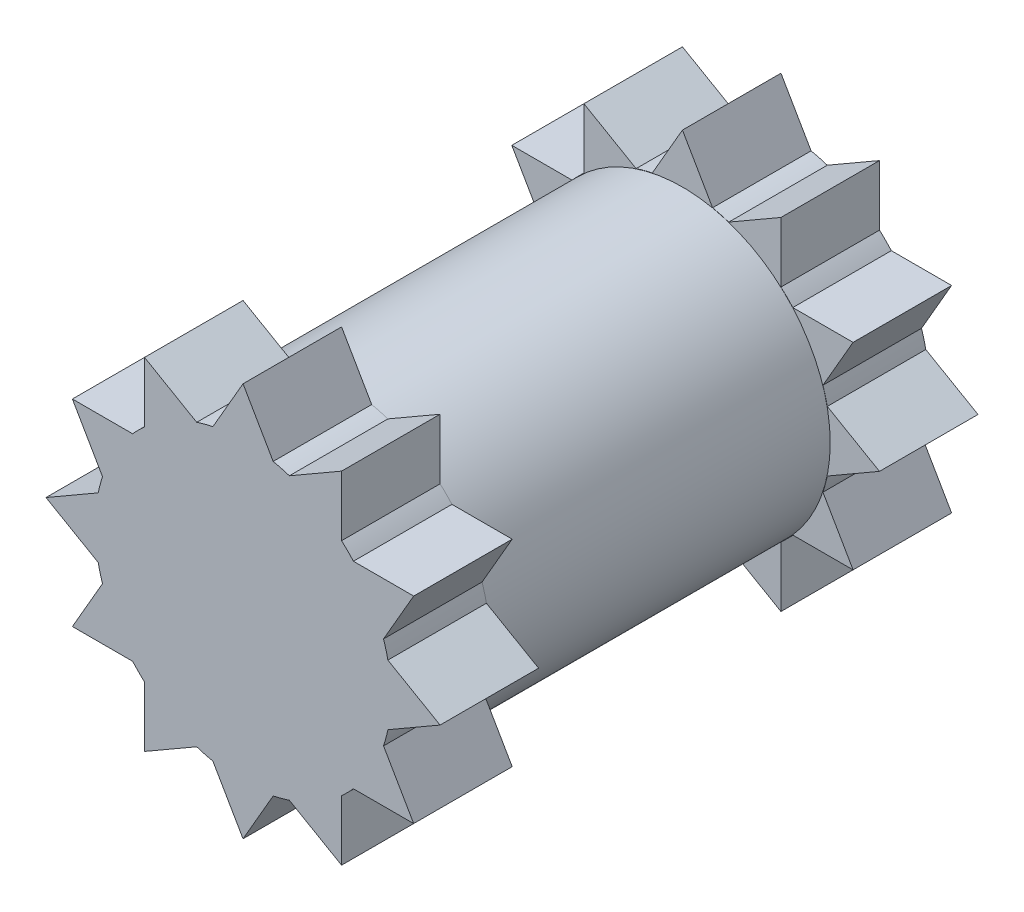
SolidWorks part; units mm, degrees
ref_plane "Ön Düzlem" through (0, 0, 0) normal (0, 0, 1) x (1, 0, 0)
ref_plane "Üst Düzlem" through (0, 0, 0) normal (0, 1, 0) x (1, 0, 0)
ref_plane "Sağ Düzlem" through (0, 0, 0) normal (1, 0, 0) x (0, 0, -1)
sketch "Çizim1" plane through (0, 0, 0) normal (0, 0, 1) x (1, 0, 0)
  circle A0 centre (0, 0) radius 2
  dimension "D1" = 4
extrude "Yükseklik-Ekstrüzyon1" add sketch "Çizim1" along normal blind 1
sketch "Çizim2" plane through (0, 0, 1) normal (0, 0, 1) x (1, 0, 0)
  circle A0 centre (0, 0) radius 1.5
  dimension "D1" = 3
extrude "Yükseklik-Ekstrüzyon2" add sketch "Çizim2" along normal blind 1.73
sketch "Çizim3" plane through (0, 0, 0) normal (0, 0, -1) x (-1, 0, 0)
  line L17 (1, 1.7321) -> (1, 1.1202)
  line L18 (0, 2) -> (0.3059, 1.4702)
  line L19 (0, 2) -> (-0.3059, 1.4702)
  line L20 (1, 1.7321) -> (0.4702, 1.4261)
  line L21 (1.7321, 1) -> (1.4261, 0.4702)
  line L22 (1.7321, 1) -> (1.1202, 1)
  line L23 (2, 0) -> (1.4702, -0.3059)
  line L24 (2, 0) -> (1.4702, 0.3059)
  line L25 (1.7321, -1) -> (1.1202, -1)
  line L26 (1.7321, -1) -> (1.4261, -0.4702)
  line L27 (1, -1.7321) -> (0.4702, -1.4261)
  line L28 (1, -1.7321) -> (1, -1.1202)
  line L29 (0, -2) -> (-0.3059, -1.4702)
  line L30 (0, -2) -> (0.3059, -1.4702)
  line L31 (-1, -1.7321) -> (-1, -1.1202)
  line L32 (-1, -1.7321) -> (-0.4702, -1.4261)
  line L33 (-1.7321, -1) -> (-1.4261, -0.4702)
  line L34 (-1.7321, -1) -> (-1.1202, -1)
  line L35 (-2, 0) -> (-1.4702, 0.3059)
  line L36 (-2, 0) -> (-1.4702, -0.3059)
  line L37 (-1.7321, 1) -> (-1.1202, 1)
  line L38 (-1.7321, 1) -> (-1.4261, 0.4702)
  line L39 (-1, 1.7321) -> (-0.4702, 1.4261)
  line L40 (-1, 1.7321) -> (-1, 1.1202)
  circle A1 centre (0, 0) radius 2 construction
  arc A17 (-1, 1.1202) -> (-1.1202, 1) centre (0, 0) ccw
  arc A18 (-0.3059, 1.4702) -> (-0.4702, 1.4261) centre (0, 0) ccw
  circle A19 centre (0, 0) radius 2
  circle A20 centre (0, 0) radius 2
  arc A21 (0.4702, 1.4261) -> (0.3059, 1.4702) centre (0, 0) ccw
  arc A22 (1.1202, 1) -> (1, 1.1202) centre (0, 0) ccw
  arc A23 (1.4702, 0.3059) -> (1.4261, 0.4702) centre (0, 0) ccw
  arc A24 (1.4261, -0.4702) -> (1.4702, -0.3059) centre (0, 0) ccw
  arc A25 (1, -1.1202) -> (1.1202, -1) centre (0, 0) ccw
  arc A26 (0.3059, -1.4702) -> (0.4702, -1.4261) centre (0, 0) ccw
  arc A27 (-0.4702, -1.4261) -> (-0.3059, -1.4702) centre (0, 0) ccw
  arc A28 (-1.1202, -1) -> (-1, -1.1202) centre (0, 0) ccw
  arc A29 (-1.4702, -0.3059) -> (-1.4261, -0.4702) centre (0, 0) ccw
  arc A30 (-1.4261, 0.4702) -> (-1.4702, 0.3059) centre (0, 0) ccw
  point P21 (0, 0)
  point P50 (0, 0)
  circle M7 centre (0, 0) radius 2
  dimension "D1" = 3.0033
  dimension "D2" = 12
  dimension "D4" = 0
extrude "Kes-Ekstrüzyon1" cut sketch "Çizim3" against normal blind 2 contours A18 L19 L39 M7 | A17 L40 L37 M7 | A30 L38 L35 M7 | A29 L36 L33 M7 | A28 L34 L31 M7 | A27 L32 L29 M7 | A26 L30 L27 M7 | A25 L28 L25 M7 | A24 L26 L23 M7 | A23 L24 L21 M7 | A22 L22 L17 M7 | A21 L20 L18 M7
ref_plane "Düzlem1" through (0, 0, 2.73) normal (0, 0, 1) x (1, 0, 0)
mirror "Aynalama3" about plane through (0, 0, 2.73) normal (0, 0, 1) of bodies 103
